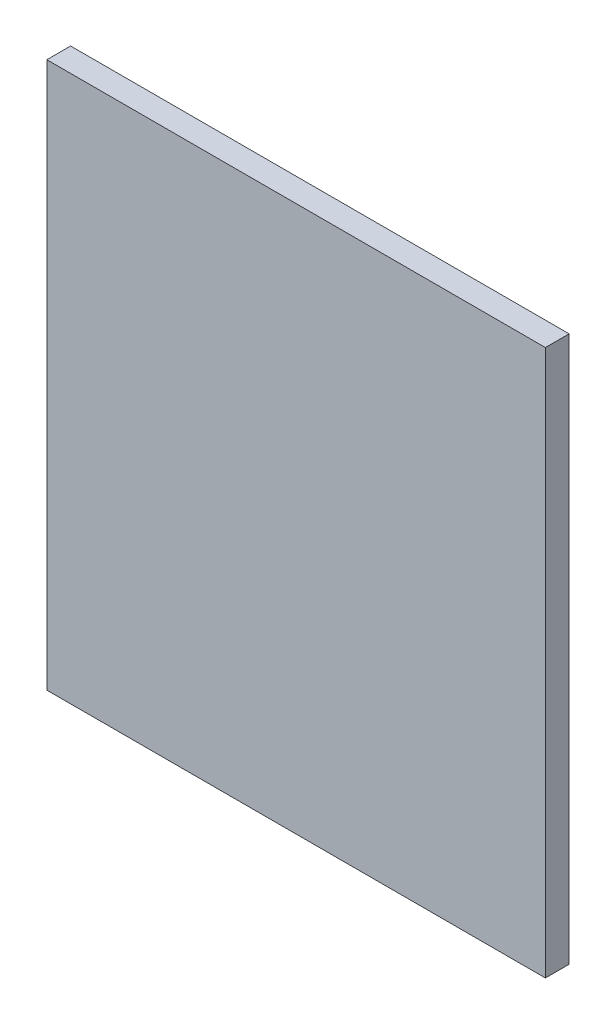
SolidWorks part; units mm, degrees
ref_plane "Front Plane" through (0, 0, 0) normal (0, 0, 1) x (1, 0, 0)
ref_plane "Top Plane" through (0, 0, 0) normal (0, 1, 0) x (1, 0, 0)
ref_plane "Right Plane" through (0, 0, 0) normal (1, 0, 0) x (0, 0, -1)
sketch "Sketch2" plane through (0, 0, 0) normal (0, 0, 1) x (1, 0, 0)
  line L1 (-133.35, 146.05) -> (133.35, 146.05)
  line L2 (-133.35, 146.05) -> (-133.35, -146.05)
  line L3 (-133.35, -146.05) -> (133.35, -146.05)
  line L4 (133.35, 146.05) -> (133.35, -146.05)
  line L5 (-133.35, 146.05) -> (133.35, -146.05) construction
  line L6 (-133.35, -146.05) -> (133.35, 146.05) construction
  point P0 (0, 0)
  dimension "D1" = 292.1
  dimension "D2" = 266.7
extrude "Boss-Extrude1" add sketch "Sketch2" along normal mid plane 12.7
